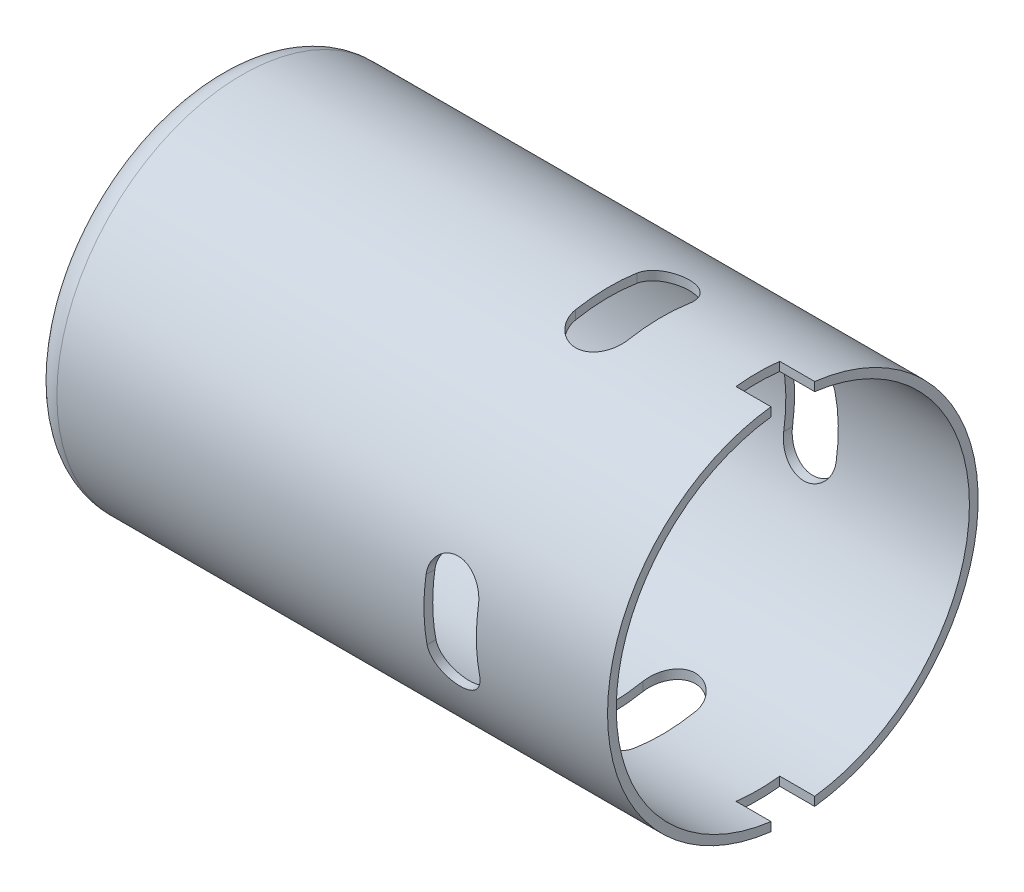
SolidWorks part; units mm, degrees
material "Chrome Stainless Steel"
ref_plane "Front" through (0, 0, 0) normal (0, 0, 1) x (1, 0, 0)
ref_plane "Top" through (0, 0, 0) normal (0, 1, 0) x (1, 0, 0)
ref_plane "Right" through (0, 0, 0) normal (1, 0, 0) x (0, 0, -1)
sketch "Sketch1" plane through (0, 0, 0) normal (0, 0, 1) x (1, 0, 0)
  line L0 (0, 0) -> (70.7, 0) construction
  line L1 (70.7, 21.2) -> (7.7, 21.2)
  line L2 (4.7, 18.2) -> (4.7, 10)
  line L3 (3.7, 9) -> (0, 9)
  line L4 (70.7, 21.2) -> (70.7, 0) construction
  line L5 (0, 9) -> (0, 0) construction
  line L6 (70.7, 20.2) -> (7.7, 20.2)
  line L7 (5.7, 18.2) -> (5.7, 8)
  line L8 (4.7, 8) -> (0, 8)
  line L9 (70.7, 21.2) -> (70.7, 20.2)
  line L10 (0, 9) -> (0, 8)
  line L11 (4.7, 18.2) -> (4.7, 9) construction
  line L12 (4.7, 9) -> (0, 9) construction
  line L13 (5.7, 8) -> (5.7, 5.5)
  line L14 (5.7, 5.5) -> (4.7, 5.5)
  line L15 (4.7, 8) -> (4.7, 5.5)
  line L16 (5.7, 8) -> (0, 8) construction
  arc A0 (7.7, 21.2) -> (4.7, 18.2) centre (7.7, 18.2) ccw
  arc A1 (7.7, 20.2) -> (5.7, 18.2) centre (7.7, 18.2) ccw
  arc A2 (4.7, 10) -> (3.7, 9) centre (3.7, 10) cw
  point P18 (4.7, 9)
  dimension "D1" = 3
  dimension "D7" = 1
  dimension "D2" = 66
  dimension "D3" = 21.2
  dimension "D4" = 9
  dimension "D5" = 4.7
  dimension "D8" = 2.5
  dimension "D6" = 1
revolve "Revolve2" add sketch "Sketch1" angle 360 about L0
sketch "Sketch2" plane through (70.7, 0, 0) normal (1, 0, 0) x (0, 0, -1)
  circle A0 centre (0, 0) radius 21.2 construction
  point P0 (0, 21.2)
ref_plane "Plane1" through (70.7, 21.2, 0) normal (0, 1, 0) x (1, 0, 0)
sketch "Sketch8" plane through (70.7, 21.2, 0) normal (0, 1, 0) x (1, 0, 0)
  line L0 (-18, 3.1531) -> (-18, -3.8469) construction
  line L1 (-15, 3.1531) -> (-15, -3.8469)
  line L2 (-21, 3.1531) -> (-21, -3.8469)
  arc A0 (-15, 3.1531) -> (-21, 3.1531) centre (-18, 3.1531) ccw
  arc A1 (-21, -3.8469) -> (-15, -3.8469) centre (-18, -3.8469) ccw
  point P2 (-18, -0.3469)
  dimension "D2" = 3
  dimension "D1" = 18
  dimension "D3" = 7
extrude "Cut-Extrude6" cut sketch "Sketch8" against normal up to next
pattern_circular "CirPattern21" count 4 over 360 about axis through (0, 0, 0) along (-1, 0, 0) of "Cut-Extrude6"
sketch "Sketch10" plane through (70.7, 21.2, 0) normal (0, 1, 0) x (1, 0, 0)
  line L0 (-4, -2.5) -> (-4, 2.5)
  line L1 (-4, 2.5) -> (0, 2.5)
  line L2 (0, 2.5) -> (0, -2.5)
  line L3 (0, -2.5) -> (-4, -2.5)
  dimension "D1" = 4
  dimension "D2" = 5
extrude "Cut-Extrude7" cut sketch "Sketch10" against normal blind 10
pattern_circular "CirPattern22" count 2 over 360 about axis through (66.7, 0, 0) along (0, 1, 0) of "Cut-Extrude7"
sketch "Sketch11" plane through (0, 0, 0) normal (0, 1, 0) x (1, 0, 0)
  line L0 (50.046, 101.3694) -> (653.3794, 101.3694) construction
sketch "Sketch12" plane through (0, 0, 0) normal (0, 1, 0) x (1, 0, 0)
  line L0 (7.6507, 101.1542) -> (610.984, 101.1542) construction
sketch "Sketch13" plane through (4.7, 0, 0) normal (-1, 0, 0) x (0, 0, 1)
  line L0 (-10.253, -10.253) -> (0, 0) construction
  line L1 (0, 0) -> (10.253, 10.253) construction
  line L2 (0, 0) -> (0, 14.5) construction
  circle A0 centre (0, 0) radius 14.5 construction
  circle A1 centre (10.253, 10.253) radius 2
  circle A2 centre (-10.253, -10.253) radius 2
  dimension "D1" = 29
  dimension "D3" = 4
  dimension "D2" = 45
extrude "Cut-Extrude8" cut sketch "Sketch13" against normal up to next contours A2 | A1
